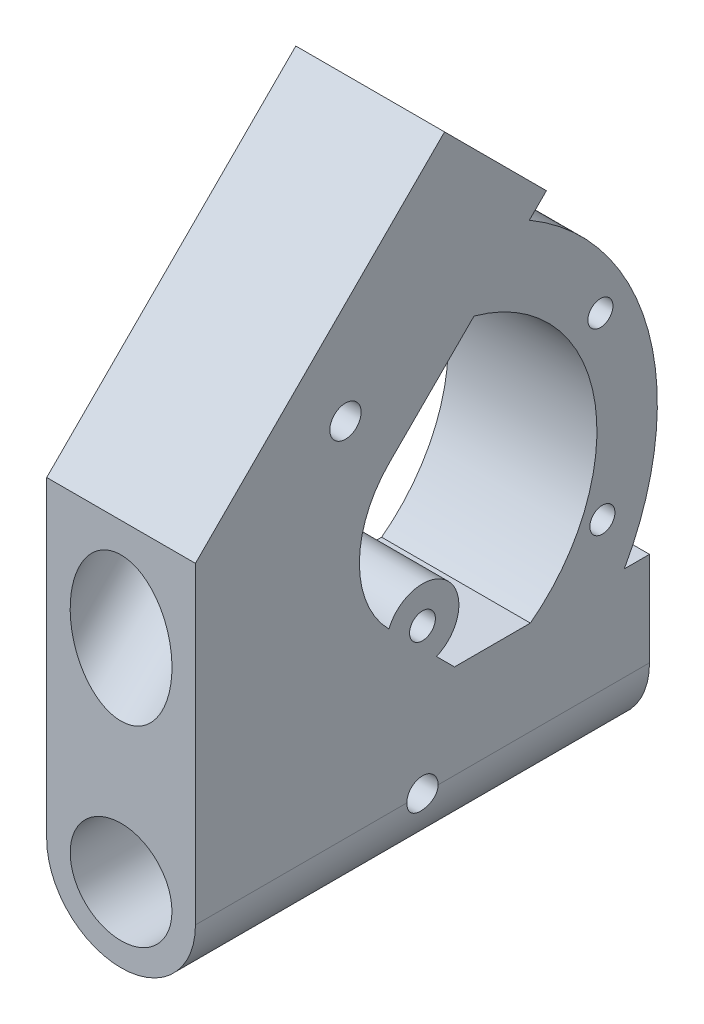
SolidWorks part; units mm, degrees
ref_plane "Alzado" through (0, 0, 0) normal (0, 0, 1) x (1, 0, 0)
ref_plane "Planta" through (0, 0, 0) normal (0, 1, 0) x (1, 0, 0)
ref_plane "Vista lateral" through (0, 0, 0) normal (1, 0, 0) x (0, 0, -1)
sketch "Croquis1" plane through (0, 0, 0) normal (0, 0, 1) x (1, 0, 0)
  line L0 (0, 0) -> (0, -10) construction
  line L4 (0, 0) -> (0, 12) construction
  line L5 (-9.5, 12) -> (9.5, 12)
  line L6 (-9.5, 12) -> (-9.5, 0)
  line L7 (9.5, 12) -> (9.5, 0)
  circle A0 centre (0, 0) radius 6.5
  arc A2 (-9.5, 0) -> (9.5, 0) centre (0, 0) ccw
  point P8 (0, -10)
  point P9 (0, 12)
  dimension "D1" = 13
  dimension "D2" = 3
  dimension "D4" = 12
extrude "Saliente-Extruir1" add sketch "Croquis1" against normal mid plane 58
sketch "Croquis2" plane through (0, 0, 0) normal (1, 0, 0) x (0, 0, -1)
  line L0 (-29, 12) -> (-29, 40)
  line L1 (-29, 40) -> (2.8198, 71.8198)
  line L2 (2.8198, 71.8198) -> (15.8306, 58.809)
  line L3 (29, 12) -> (-29, 12) construction
  line L4 (-29, 12) -> (4.0901, 12)
  line L5 (15.8306, 58.809) -> (-4.2518, 38.7267)
  line L6 (-4.2518, 20.3419) -> (4.0901, 12)
  arc A0 (-4.2518, 20.3419) -> (-4.2518, 38.7267) centre (4.9406, 29.5343) cw
  dimension "D4" = 135
  dimension "D5" = 13
  dimension "D1" = 28
  dimension "D2" = 45
  dimension "D3" = 18.4
extrude "Saliente-Extruir2" add sketch "Croquis2" along normal mid plane 19
ref_plane "Plano1" through (0, 37.3198, -37.3198) normal (0, 0.7071, -0.7071) x (-1, 0, 0)
sketch "Croquis3" plane through (0, 37.3198, -37.3198) normal (0, 0.7071, -0.7071) x (1, 0, 0)
  line L0 (0, -48.7904) -> (0, -30.3904) construction
  line L1 (9.5, -48.7904) -> (-9.5, -48.7904) construction
  line L4 (9.5, -30.3904) -> (-9.5, -30.3904) construction
  circle A0 centre (0, -39.5904) radius 6.5
  dimension "D1" = 13
extrude "Cortar-Extruir1" cut sketch "Croquis3" against normal blind 73
sketch "Croquis4" plane through (0, 0, 0) normal (1, 0, 0) x (0, 0, -1)
  line L0 (-4.2518, 38.7267) -> (15.8306, 58.809) construction
  line L1 (29, 12) -> (4.0901, 12) construction
  line L2 (6.5823, 49.5608) -> (13.6534, 56.6319)
  line L3 (13.7825, 12) -> (25.7825, 12)
  line L4 (15.8306, 58.809) -> (2.8198, 71.8198) construction
  line L5 (29, 0) -> (29, 12) construction
  arc A0 (6.5823, 49.5608) -> (13.7825, 12) centre (1, 29.0202) cw
  arc A1 (13.6534, 56.6319) -> (25.7825, 12) centre (-3, 28.1421) cw
  dimension "D3" = 33
  dimension "D4" = 4
  dimension "D5" = 35
  dimension "D6" = 32
  dimension "D1" = 10
  dimension "D2" = 12
extrude "Saliente-Extruir3" add sketch "Croquis4" along normal mid plane 19
sketch "Croquis5" plane through (0, 0, 0) normal (1, 0, 0) x (0, 0, -1)
  circle A0 centre (0, 18.5926) radius 4.65
  circle A1 centre (0, 18.5926) radius 1.65
  dimension "D1" = 3.3
  dimension "D2" = 3
extrude "Saliente-Extruir4" add sketch "Croquis5" along normal mid plane 19 contours A0
sketch "Croquis6" plane through (0, 0, 0) normal (1, 0, 0) x (0, 0, -1)
  circle A0 centre (22.7263, 41.8254) radius 1.6
  circle A1 centre (22.98, 18.8454) radius 1.6
  circle A2 centre (0, 18.5926) radius 1.65 construction
  dimension "D1" = 3.2
  dimension "D2" = 22.98
  dimension "D3" = 32.5
  dimension "D4" = 22.98
extrude "Cortar-Extruir2" cut sketch "Croquis6" against normal mid plane 30 contours A0 | A1
sketch "Croquis7" plane through (0, 0, 0) normal (1, 0, 0) x (0, 0, -1)
  line L0 (9.3252, 65.3144) -> (-29, 26.9892) construction
  line L1 (15.8306, 58.809) -> (2.8198, 71.8198) construction
  line L2 (-29, 40) -> (-29, 0) construction
  circle A0 centre (0, 0) radius 2
  circle A2 centre (-9.8374, 46.1518) radius 2
  dimension "D1" = 4
extrude "Cortar-Extruir3" cut sketch "Croquis7" against normal mid plane 53
